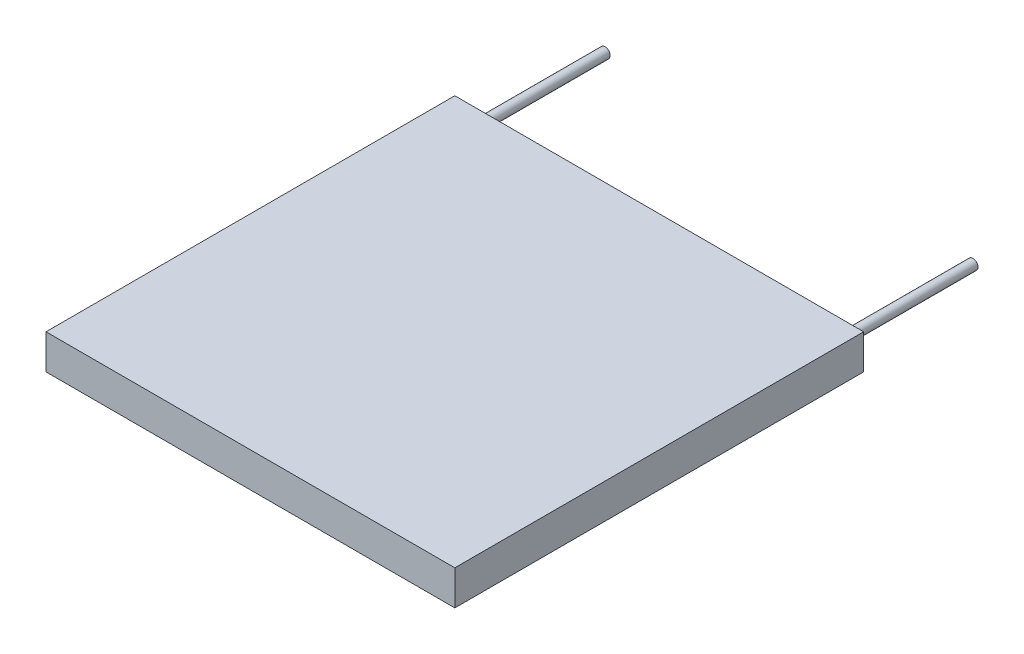
SolidWorks part; units mm, degrees
ref_plane "Front Plane" through (0, 0, 0) normal (0, 0, 1) x (1, 0, 0)
ref_plane "Top Plane" through (0, 0, 0) normal (0, 1, 0) x (1, 0, 0)
ref_plane "Right Plane" through (0, 0, 0) normal (1, 0, 0) x (0, 0, -1)
sketch "Sketch1" plane through (0, 0, 0) normal (0, 1, 0) x (1, 0, 0)
  line L1 (-50.6719, 27.0595) -> (-10.6719, 27.0595)
  line L2 (-50.6719, 27.0595) -> (-50.6719, -12.9405)
  line L3 (-50.6719, -12.9405) -> (-10.6719, -12.9405)
  line L4 (-10.6719, 27.0595) -> (-10.6719, -12.9405)
  dimension "D1" = 40
  dimension "D2" = 40
extrude "Boss-Extrude1" add sketch "Sketch1" along normal blind 3.4
sketch "Sketch2" plane through (0, 0, -27.0595) normal (0, 0, -1) x (-1, 0, 0)
  line L0 (10.6719, 3.4) -> (50.6719, 3.4) construction
  line L1 (50.6719, 3.4) -> (50.6719, 0) construction
  circle A1 centre (48.6719, 1.7) radius 0.5
  dimension "D4" = 1
  dimension "D2" = 1.7
  dimension "D5" = 2
extrude "Boss-Extrude2" add sketch "Sketch2" along normal blind 12.7
sketch "Sketch3" plane through (0, 0, -27.0595) normal (0, 0, -1) x (-1, 0, 0)
  line L0 (10.6719, 3.4) -> (10.6719, 0) construction
  circle A0 centre (12.6785, 1.772) radius 0.4953
  dimension "D1" = 0.9906
  dimension "D2" = 2.0066
extrude "Boss-Extrude3" add sketch "Sketch3" along normal blind 12.7
